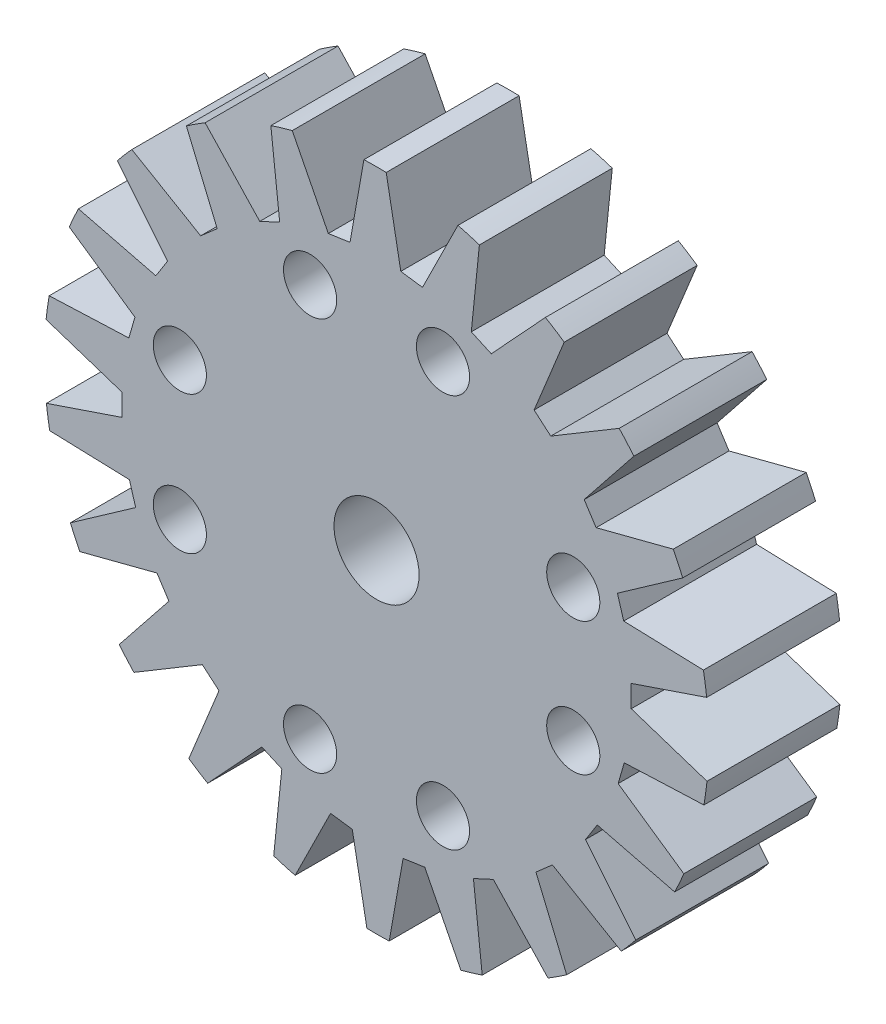
SolidWorks part; units mm, degrees
other "Markup1"
sketch "Sketch3" plane through (-11.5, 11.4999, 3) normal (-0.0441, 0.0247, 0.9987) x (0.9973, -0.0583, 0.0455)
ref_plane "Front Plane" through (0, 0, 0) normal (0, 0, 1) x (1, 0, 0)
ref_plane "Top Plane" through (0, 0, 0) normal (0, 1, 0) x (1, 0, 0)
ref_plane "Right Plane" through (0, 0, 0) normal (1, 0, 0) x (0, 0, -1)
sketch "Sketch1" plane through (0, 0, 0) normal (0, 0, 1) x (1, 0, 0)
  line L2 (-2.5, 7.4) -> (2.5, 7.4) construction
  line L3 (-2.5, -7.4) -> (2.5, -7.4) construction
  line L4 (-7.4, -2.694) -> (-7.4, 2.5) construction
  line L5 (7.4, -2.5) -> (7.4, 2.5) construction
  circle A0 centre (0, 0) radius 12.5
  circle A1 centre (0, 0) radius 10.5 construction
  circle A2 centre (0, 0) radius 1.6
  circle A6 centre (2.5, -7.4) radius 1
  circle A8 centre (-2.5, -7.4) radius 1
  circle A9 centre (7.4, -2.5) radius 1
  circle A10 centre (-7.4, -2.694) radius 1
  circle A11 centre (-7.4, 2.5) radius 1
  circle A12 centre (-2.5, 7.4) radius 1
  circle A13 centre (2.5, 7.4) radius 1
  circle A14 centre (7.4, 2.5) radius 1
  point P5 (0, 0)
  point P8 (0, 0)
  point P11 (0, 0)
  point P14 (-8.1064, -2.694)
  point P18 (0, 0)
  point P19 (0, 0)
  point P26 (-7.8477, 2.5)
  point P27 (0, 0)
  point P31 (-2.832, 7.4)
  point P32 (0, 0)
  point P33 (0, 0)
  point P36 (0, 0)
  point P37 (0, 0)
  point P40 (0, 0)
  dimension "D1" = 25
  dimension "D2" = 21
  dimension "D3" = 2.5
  dimension "3,2" = 3.2
  dimension "D4" = 5
  dimension "D5" = 5
extrude "Boss-Extrude1" add sketch "Sketch1" along normal blind 5
sketch "Sketch2" plane through (0, 0, 5) normal (0, 0, 1) x (1, 0, 0)
  line L1 (-9.205, 8.4568) -> (-6.6167, 6.9401)
  line L2 (-6.6167, 6.9401) -> (-5.9956, 7.4831)
  line L3 (-5.9956, 7.4831) -> (-7.1537, 10.2506)
  line L4 (-6.6167, 6.9401) -> (-8.9503, 4.8994) construction
  line L5 (-8.9503, 4.8994) -> (-10.1083, 7.6669) construction
  line L6 (-10.1083, 7.6669) -> (-9.205, 8.4568) construction
  line L7 (-7.1537, 10.2506) -> (-7.4561, 10.5965)
  line L9 (-7.4561, 10.5965) -> (-9.5074, 8.8027)
  line L10 (-9.205, 8.4568) -> (-9.5074, 8.8027)
  circle A0 centre (0, 0) radius 11.0385 construction
  circle A1 centre (0, 0) radius 12.5 construction
  point P11 (-6.5746, 8.8669)
  point P12 (-7.9108, 7.6985)
  dimension "D1" = 2.725
  dimension "D2" = 0.825
  dimension "D4" = 3
  dimension "D5" = 3.1
  dimension "D6" = 1.2
extrude "Cut-Extrude1" cut sketch "Sketch2" against normal through all
pattern_circular "CirPattern1" count 22 over 360 about axis through (0, 0, 0) along (0, 0, 1) of "Cut-Extrude1"
